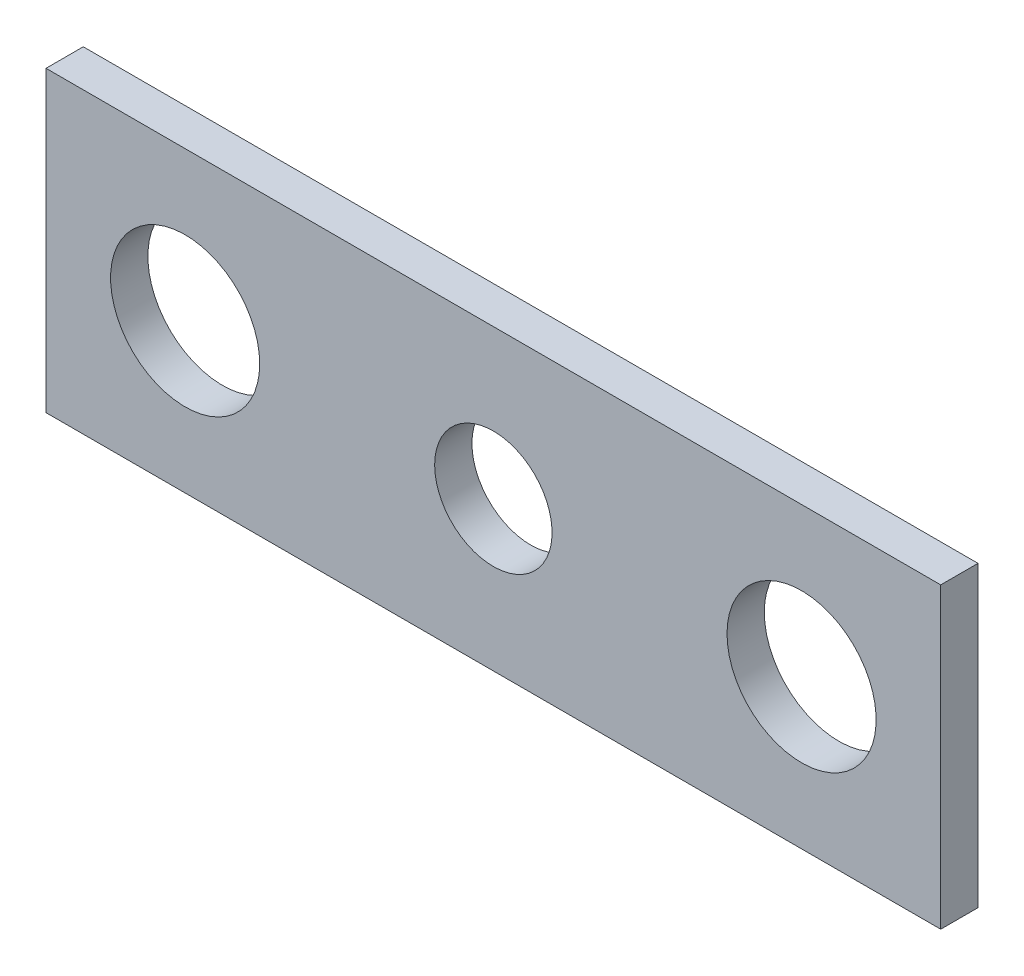
SolidWorks part; units mm, degrees
ref_plane "Front Plane" through (0, 0, 0) normal (0, 0, 1) x (1, 0, 0)
ref_plane "Top Plane" through (0, 0, 0) normal (0, 1, 0) x (1, 0, 0)
ref_plane "Right Plane" through (0, 0, 0) normal (1, 0, 0) x (0, 0, -1)
sketch "Sketch1" plane through (0, 0, 0) normal (0, 0, 1) x (1, 0, 0)
  line L1 (0, 0) -> (-152.4, 0)
  line L2 (0, 0) -> (0, 50.8)
  line L3 (0, 50.8) -> (-152.4, 50.8)
  line L4 (-152.4, 0) -> (-152.4, 50.8)
  dimension "D1" = 50.8
  dimension "D2" = 152.4
extrude "Boss-Extrude1" add sketch "Sketch1" along normal blind 6.35
sketch "Sketch2" plane through (0, 0, 0) normal (0, 0, -1) x (-1, 0, 0)
  line L0 (76.2, 54.4848) -> (76.2, 3.6848) construction
  line L3 (152.4, 0) -> (0, 0) construction
  line L4 (0, 50.8) -> (152.4, 50.8) construction
  circle A0 centre (23.7, 25.4) radius 12.7
  circle A1 centre (76.2, 25.4) radius 10
  circle A2 centre (128.7, 25.4) radius 12.7
  point P13 (76.2, 50.8)
  dimension "D1" = 25.4
  dimension "D2" = 20
  dimension "D3" = 52.5
  dimension "D4" = 25.4
extrude "Cut-Extrude1" cut sketch "Sketch2" against normal blind 6.35 contours A0 | A1 | A2
